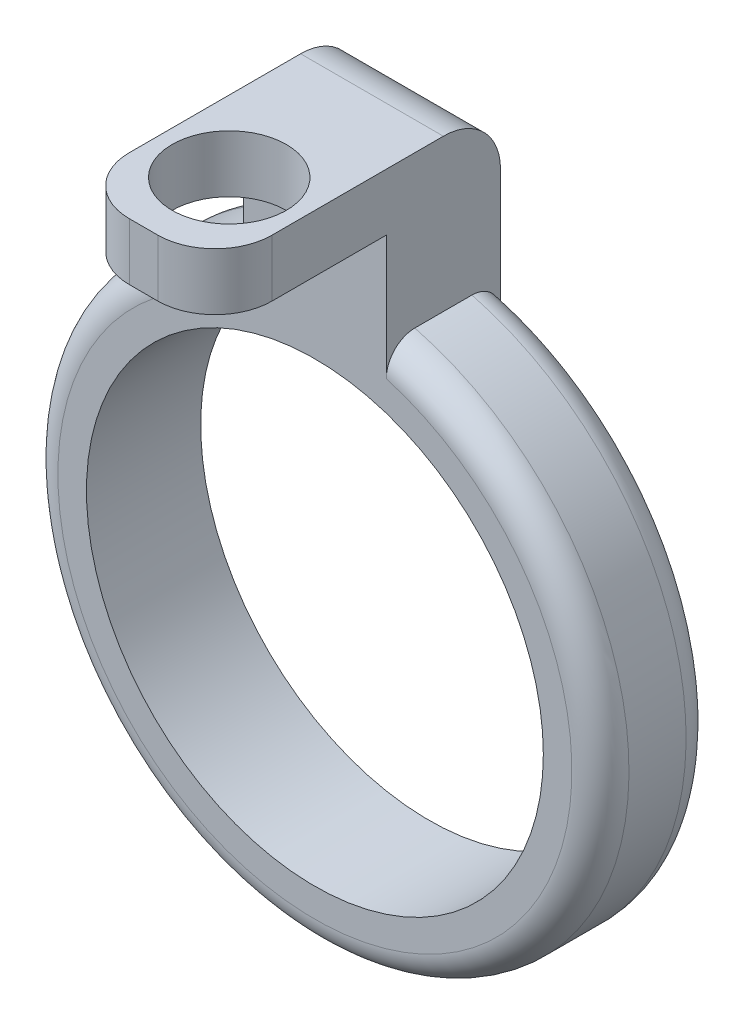
SolidWorks part; units mm, degrees
ref_plane "Front Plane" through (0, 0, 0) normal (0, 0, 1) x (1, 0, 0)
ref_plane "Top Plane" through (0, 0, 0) normal (0, 1, 0) x (1, 0, 0)
ref_plane "Right Plane" through (0, 0, 0) normal (1, 0, 0) x (0, 0, -1)
sketch "Sketch1" plane through (0, 0, 0) normal (0, 0, 1) x (1, 0, 0)
  line L0 (0, 0) -> (-261.777, -170) construction
  line L1 (0, 0) -> (202.5981, -170) construction
  line L2 (202.5981, -170) -> (202.5981, -64.2604) construction
  line L3 (-261.777, -170) -> (-261.777, -270) construction
  line L4 (202.5981, -170) -> (438.223, -170) construction
  line L5 (202.5981, -170) -> (91.5369, -270) construction
  line L6 (-286.777, -145) -> (-286.777, -195) construction
  line L7 (438.223, -170) -> (438.223, -270) construction
  line L8 (-236.777, -145) -> (-236.777, -195) construction
  line L9 (-286.777, -195) -> (-236.777, -195) construction
  line L10 (-236.777, -145) -> (-286.777, -145) construction
  line L11 (-261.777, -570) -> (438.223, -570) construction
  line L12 (-261.777, -670) -> (91.5369, -670) construction
  circle A0 centre (-261.777, -270) radius 50 construction
  circle A1 centre (-261.777, -270) radius 40 construction
  circle A2 centre (91.5369, -270) radius 40 construction
  circle A3 centre (91.5369, -270) radius 50 construction
  circle A4 centre (438.223, -270) radius 40 construction
  circle A5 centre (438.223, -270) radius 50 construction
  circle A6 centre (0, 0) radius 32.5 construction
  circle A7 centre (202.5981, -170) radius 25 construction
  point P13 (-286.777, -170)
  dimension "D7" = 80
  dimension "D8" = 100
  dimension "D13" = 65
  dimension "D14" = 50
  dimension "D1" = 50
  dimension "D2" = 107
  dimension "D3" = 170
  dimension "D4" = 100
  dimension "D5" = 48
  dimension "D6" = 700
  dimension "D9" = 25
  dimension "D10" = 50
  dimension "D11" = 400
  dimension "D12" = 100
sketch "Sketch2" plane through (0, 0, 0) normal (0, 0, 1) x (1, 0, 0)
  line L0 (-286.777, -195) -> (-236.777, -195) construction
  line L1 (-274.277, -195) -> (-249.277, -195)
  line L2 (-274.277, -195) -> (-274.277, -200)
  line L3 (-274.277, -200) -> (-249.277, -200)
  line L4 (-249.277, -195) -> (-249.277, -200)
  circle A0 centre (-261.777, -270) radius 40
  circle A1 centre (-261.777, -270) radius 50
  circle A2 centre (-261.777, -270) radius 40 construction
  circle A3 centre (-261.777, -270) radius 50 construction
  point P14 (-261.777, -195)
  dimension "D1" = 25
  dimension "D2" = 5
extrude "Boss-Extrude1" add sketch "Sketch2" along normal mid plane 20
sketch "Sketch3" plane through (0, -200, 0) normal (0, -1, 0) x (1, 0, 0)
  line L4 (-274.277, -10) -> (-249.277, -10)
  line L5 (-249.277, -10) -> (-249.277, 10)
  line L6 (-249.277, 10) -> (-274.277, 10)
  line L7 (-274.277, 10) -> (-274.277, -10)
  line L8 (-274.277, -10) -> (-249.277, -10)
  line L9 (-249.277, -10) -> (-249.277, 10)
  line L10 (-249.277, 10) -> (-274.277, 10)
  line L11 (-274.277, 10) -> (-274.277, -10)
  dimension "D1" = 0
extrude "Boss-Extrude2" add sketch "Sketch3" along normal up to next
sketch "Sketch4" plane through (0, 0, 10) normal (0, 0, 1) x (1, 0, 0)
  line L0 (-249.277, -221.5877) -> (-249.277, -195) construction
  line L1 (-274.277, -195) -> (-249.277, -195)
  line L2 (-274.277, -195) -> (-274.277, -205)
  line L3 (-274.277, -205) -> (-249.277, -205)
  line L4 (-249.277, -195) -> (-249.277, -205)
  dimension "D1" = 10
extrude "Boss-Extrude3" add sketch "Sketch4" along normal blind 30
sketch "Sketch5" plane through (0, -205, 0) normal (0, -1, 0) x (1, 0, 0)
  line L0 (-274.277, 40) -> (-249.277, 10) construction
  circle A0 centre (-261.777, 25) radius 10
  dimension "D1" = 20
extrude "Cut-Extrude1" cut sketch "Sketch5" against normal up to next
fillet "Fillet1" radius 10 2 edges at (-249.277, -200, 40) (-274.277, -200, 40)
fillet "Fillet2" radius 10 1 edges at (-261.777, -195, -10)
fillet "Fillet3" radius 5 2 edges at (-261.777, -320, -10) (-261.777, -320, 10)
